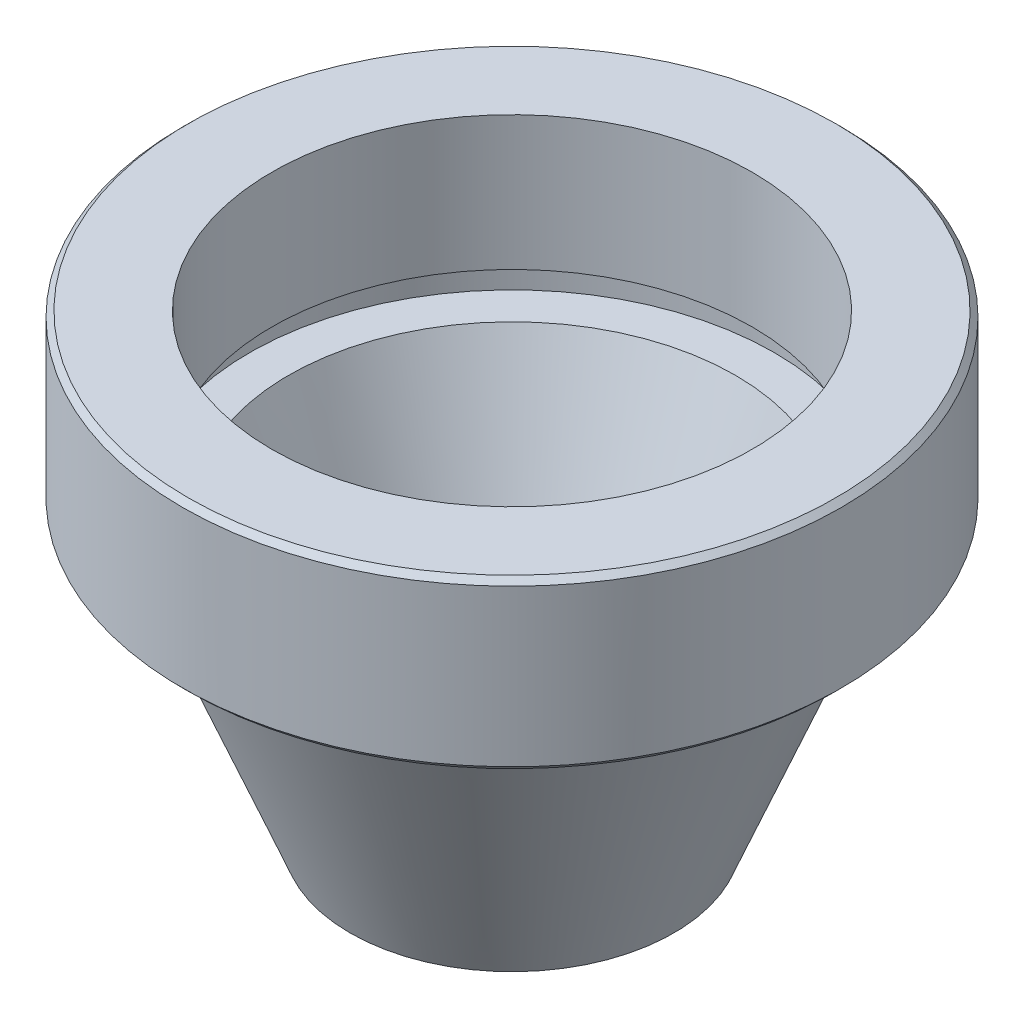
SolidWorks part; units mm, degrees
material "Cobre"
ref_plane "Plano frontal" through (0, 0, 0) normal (0, 0, 1) x (1, 0, 0)
ref_plane "Plano superior" through (0, 0, 0) normal (0, 1, 0) x (1, 0, 0)
ref_plane "Plano direito" through (0, 0, 0) normal (1, 0, 0) x (0, 0, -1)
sketch "Esboço1" plane through (0, 0, 0) normal (1, 0, 0) x (0, 0, -1)
  line L0 (0, 0) -> (0, 20) construction
  line L1 (23.5, 20) -> (20, 20)
  line L2 (25, 20) -> (14.4953, -6)
  line L3 (14.4953, -6) -> (9.4953, -6)
  line L4 (20, 20) -> (9.4953, -6)
  line L5 (25, 20) -> (29.5, 20)
  line L6 (29.5, 35) -> (21.5, 35)
  line L7 (29.5, 20) -> (29.5, 35)
  line L8 (21.5, 23) -> (21.5, 35)
  line L9 (21.5, 23) -> (23.5, 23)
  line L10 (23.5, 23) -> (23.5, 20)
  dimension "D1" = 50
  dimension "D2" = 26
  dimension "D3" = 68
  dimension "D4" = 40
  dimension "D5" = 8
  dimension "D6" = 43
  dimension "D7" = 3
  dimension "D8" = 12
  dimension "D9" = 2
revolve "Revolução1" add sketch "Esboço1" angle 360 about L0
cosmetic thread "Representação de rosca1" parameters "D2"=45
chamfer "Chanfro1" distance 0.5 angle 45 2 edges at (0, 20, -29.5) (0, 35, -29.5)
fillet "Filete1" radius 3 1 edges at (0, 20, -25)
